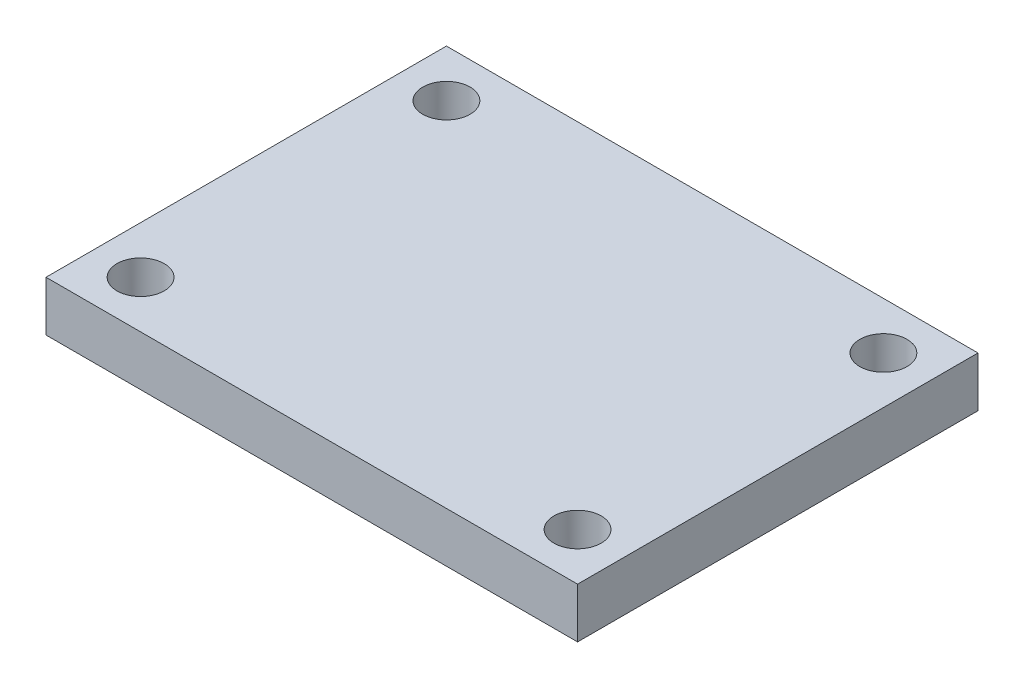
SolidWorks part; units mm, degrees
ref_plane "Alzado" through (0, 0, 0) normal (0, 0, 1) x (1, 0, 0)
ref_plane "Planta" through (0, 0, 0) normal (0, 1, 0) x (1, 0, 0)
ref_plane "Vista lateral" through (0, 0, 0) normal (1, 0, 0) x (0, 0, -1)
sketch "Croquis1" plane through (0, 0, 0) normal (0, 1, 0) x (1, 0, 0)
  line L1 (16.8592, -12.7) -> (-16.8593, -12.7)
  line L2 (16.8592, -12.7) -> (16.8592, 12.7)
  line L3 (16.8592, 12.7) -> (-16.8593, 12.7)
  line L4 (-16.8593, -12.7) -> (-16.8593, 12.7)
  line L5 (16.8592, -12.7) -> (-16.8593, 12.7) construction
  line L6 (16.8592, 12.7) -> (-16.8593, -12.7) construction
  point P0 (0, 0)
  dimension "D1" = 33.7185
  dimension "D2" = 25.4
extrude "Saliente-Extruir1" add sketch "Croquis1" along normal blind 3.175
ref_plane "Plano1" through (0, 0, 0) normal (0, 0, 1) x (1, 0, 0)
sketch "Croquis3" plane through (0, 3.175, 0) normal (0, 1, 0) x (1, 0, 0)
  line L0 (-16.8592, 0) -> (16.8593, 0) construction
  line L1 (-16.8593, 12.7) -> (-16.8593, -12.7) construction
  line L2 (-16.8593, 12.7) -> (-16.8593, -12.7) construction
  line L4 (16.8592, 12.7) -> (-16.8593, 12.7) construction
  line L5 (0, 12.7) -> (0, -12.7) construction
  line L6 (-16.8593, -12.7) -> (16.8592, -12.7) construction
  line L7 (16.8592, -12.7) -> (16.8592, 12.7) construction
  circle A0 centre (-13.8593, 9.7) radius 1.5
  circle A1 centre (-13.8592, -23.336) radius 1.5
  circle A2 centre (13.8592, -23.336) radius 1.5
  circle A3 centre (13.8593, 9.7) radius 1.5
  circle A4 centre (13.8593, -9.7) radius 1.5
  circle A5 centre (-13.8593, -9.7) radius 1.5
  dimension "D1" = 3
  dimension "D2" = 3
  dimension "D3" = 3
extrude "Cortar-Extruir1" cut sketch "Croquis3" against normal blind 10
